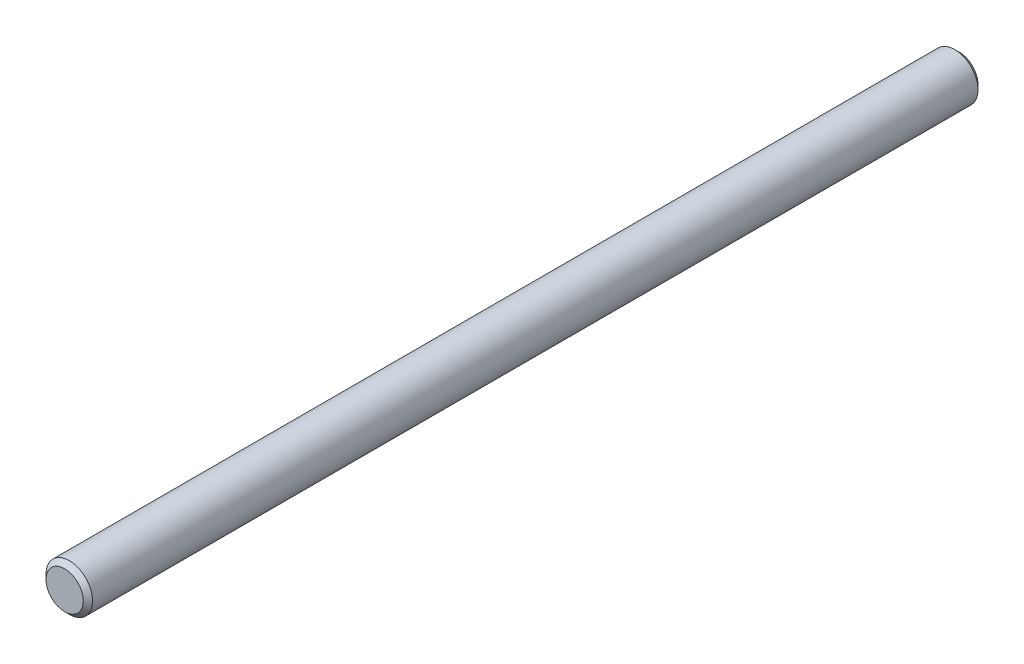
SolidWorks part; units mm, degrees
ref_plane "Front" through (0, 0, 0) normal (0, 0, 1) x (1, 0, 0)
ref_plane "Top" through (0, 0, 0) normal (0, 1, 0) x (1, 0, 0)
ref_plane "Right" through (0, 0, 0) normal (1, 0, 0) x (0, 0, -1)
sketch "Sketch1" plane through (0, 0, 0) normal (0, 0, 1) x (1, 0, 0)
  circle A0 centre (0, 0) radius 3.9688 construction
  dimension "Diameter" = 7.9375
sketch "Sketch2" plane through (0, 0, 0) normal (1, 0, 0) x (0, 0, -1)
  line L0 (-76.2, 0) -> (76.2, 0) construction
  line L1 (5.2388, 0) -> (-5.2388, 0) construction
  line L3 (76.2, 3.9687) -> (76.2, -3.9688) construction
  line L4 (-76.2, 3.9688) -> (-76.2, -3.9687) construction
  line L5 (-66.2781, 3.9688) -> (-66.2781, -3.9688) construction
  line L6 (66.2781, 3.9688) -> (66.2781, -3.9688) construction
  point P6 (0, 0)
  point P10 (76.2, 0)
  point P13 (-76.2, 0)
  point P16 (-66.2781, 0)
  point P19 (66.2781, 0)
  dimension "D1" = 7.9375
  dimension "Length" = 152.4
  dimension "D2" = 9.9219
  dimension "D3" = 9.9219
sketch "Sketch3" plane through (0, 0, 0) normal (0, 0, 1) x (1, 0, 0)
  line L0 (0, 3.9688) -> (0, -3.9687) construction
  circle A0 centre (0, 0) radius 3.9688
  dimension "D1" = 7.9375
extrude "Boss-Extrude1" add sketch "Sketch3" along normal mid plane 152.4
chamfer "Chamfer1" distance 0.7937 angle 45 2 edges at (3.9688, 0, -76.2) (3.9688, 0, 76.2)
equation "\"D1@Sketch2\" = \"Diameter@Sketch1\""
equation "\"D1@Sketch3\" = \"Diameter@Sketch1\""
equation "\"D1@Boss-Extrude1\" = \"Length@Sketch2\""
equation "\"D1@Chamfer1\" = \"Diameter@Sketch1\" * .1"
equation "\"D2@Sketch2\"=\"Diameter@Sketch1\"*1.25"
equation "\"D3@Sketch2\"=\"D2@Sketch2\""
